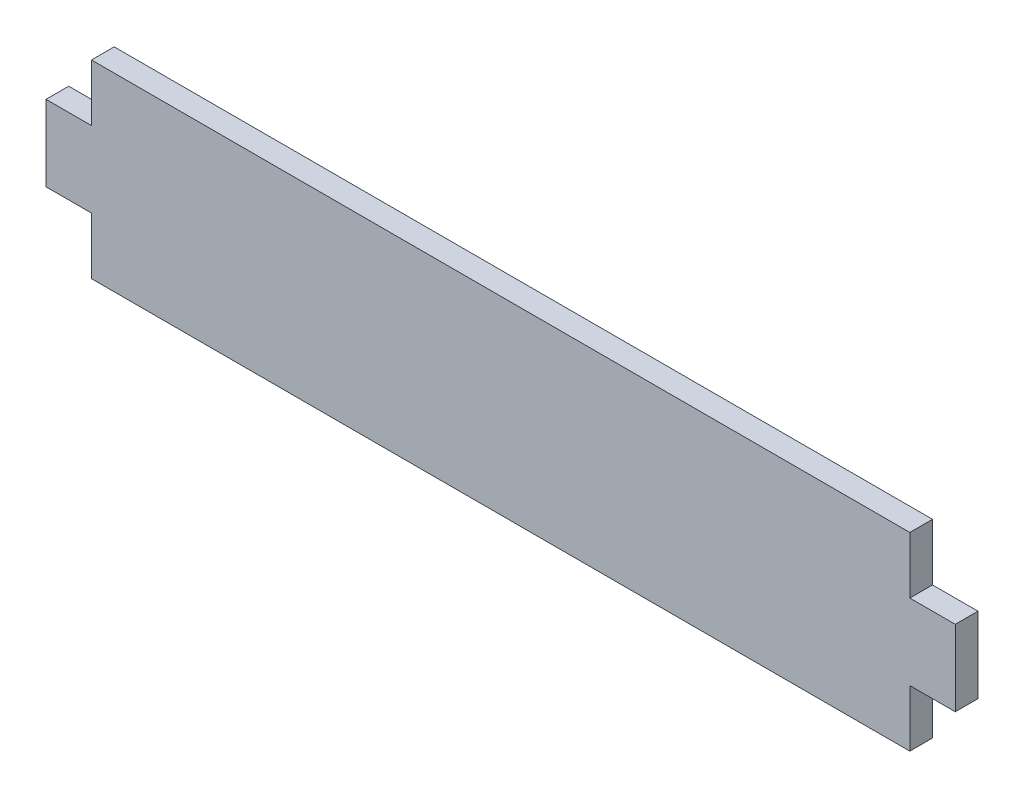
SolidWorks part; units mm, degrees
ref_plane "Front Plane" through (0, 0, 0) normal (0, 0, 1) x (1, 0, 0)
ref_plane "Top Plane" through (0, 0, 0) normal (0, 1, 0) x (1, 0, 0)
ref_plane "Right Plane" through (0, 0, 0) normal (1, 0, 0) x (0, 0, -1)
sketch "Sketch1" plane through (0, 0, 0) normal (0, 0, 1) x (1, 0, 0)
  line L0 (55, 0) -> (-55, 0) construction
  line L1 (54, 12.5) -> (-54, 12.5)
  line L2 (54, 12.5) -> (54, 5)
  line L3 (54, -12.5) -> (-54, -12.5)
  line L4 (-54, 12.5) -> (-54, 5)
  line L5 (54, 12.5) -> (-54, -12.5) construction
  line L6 (54, -12.5) -> (-54, 12.5) construction
  line L7 (0, -12.5) -> (0, 12.5) construction
  line L8 (54, -5) -> (54, -12.5)
  line L9 (60, 5) -> (54, 5)
  line L10 (60, 5) -> (60, -5)
  line L11 (60, -5) -> (54, -5)
  line L13 (60, 5) -> (54, -5) construction
  line L14 (60, -5) -> (54, 5) construction
  line L15 (-60, -5) -> (-54, -5)
  line L16 (-60, 5) -> (-60, -5)
  line L17 (-60, 5) -> (-54, 5)
  line L18 (-54, -5) -> (-54, -12.5)
  point P0 (0, 0)
  point P6 (57, 0)
  point P9 (0, 0)
  point P12 (0, 0)
  dimension "D1" = 25
  dimension "D2" = 108
  dimension "D3" = 10
  dimension "D4" = 6
  dimension "D5" = 7.5
extrude "Boss-Extrude1" add sketch "Sketch1" along normal blind 3
